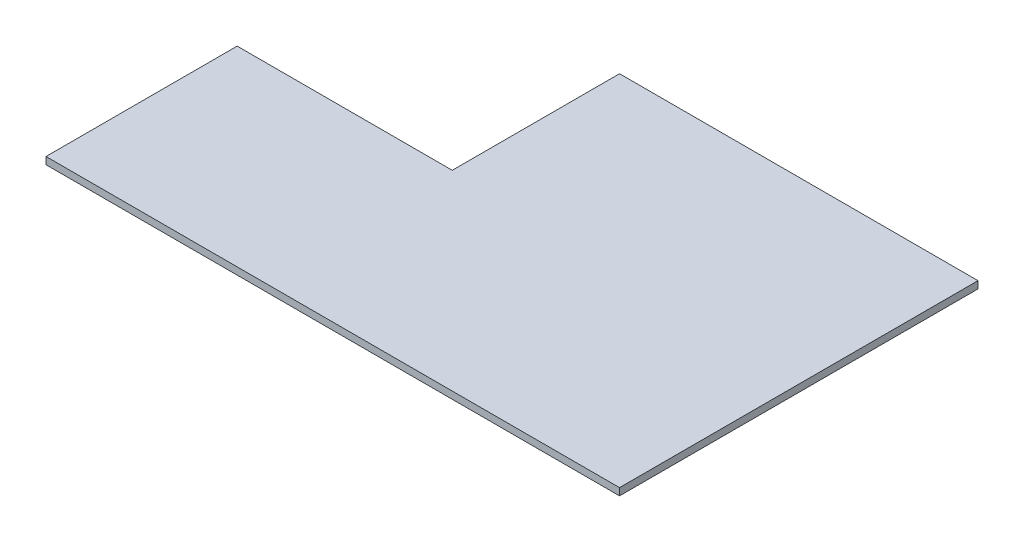
SolidWorks part; units mm, degrees
ref_plane "Front Plane" through (0, 0, 0) normal (0, 0, 1) x (1, 0, 0)
ref_plane "Top Plane" through (0, 0, 0) normal (0, 1, 0) x (1, 0, 0)
ref_plane "Right Plane" through (0, 0, 0) normal (1, 0, 0) x (0, 0, -1)
sketch "Sketch1" plane through (0, 0, 0) normal (0, 1, 0) x (1, 0, 0)
  line L0 (120, 132.069) -> (120, -17.931)
  line L1 (-120, 62.069) -> (-30, 62.069)
  line L2 (-120, 62.069) -> (-120, -17.931)
  line L3 (-120, -17.931) -> (120, -17.931)
  line L9 (120, 132.069) -> (-30, 132.069)
  line L10 (-30, 62.069) -> (-30, 132.069)
  point P0 (0, 0)
  dimension "D1" = 240
  dimension "D2" = 70
  dimension "D3" = 80
  dimension "D4" = 90
extrude "Boss-Extrude1" add sketch "Sketch1" along normal blind 3
